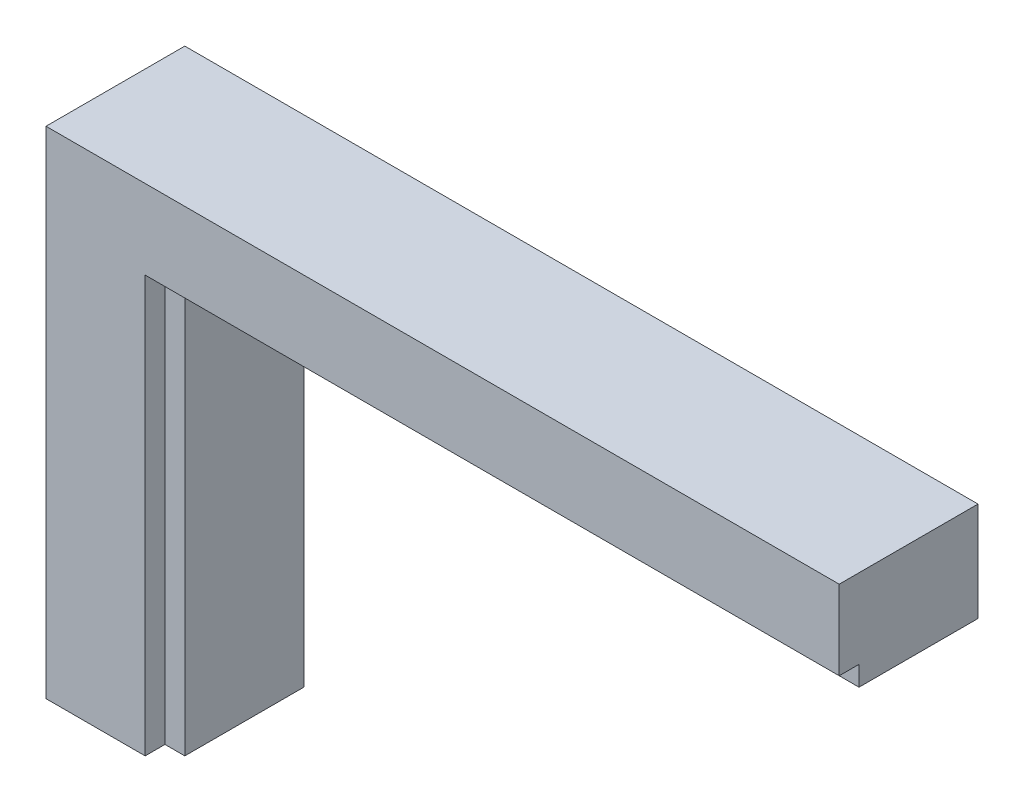
SolidWorks part; units mm, degrees
ref_plane "Спереди" through (0, 0, 0) normal (0, 0, 1) x (1, 0, 0)
ref_plane "Сверху" through (0, 0, 0) normal (0, 1, 0) x (1, 0, 0)
ref_plane "Справа" through (0, 0, 0) normal (1, 0, 0) x (0, 0, -1)
sketch "Эскиз2" plane through (0, 0, 0) normal (0, 0, 1) x (1, 0, 0)
  line L0 (0, 0) -> (0, 250)
  line L1 (0, 250) -> (400, 250)
  line L2 (400, 250) -> (400, 200)
  line L3 (400, 200) -> (60, 200)
  line L4 (60, 200) -> (60, 0)
  line L5 (60, 0) -> (0, 0)
extrude "Бобышка-Вытянуть1" add sketch "Эскиз2" along normal blind 70
sketch "Эскиз3" plane through (0, 0, 0) normal (0, -1, 0) x (1, 0, 0)
  line L1 (60, 70) -> (50, 70)
  line L2 (60, 70) -> (60, 60)
  line L3 (60, 60) -> (50, 60)
  line L4 (50, 70) -> (50, 60)
extrude "Вырез-Вытянуть1" cut sketch "Эскиз3" against normal blind 210
sketch "Эскиз4" plane through (400, 0, 0) normal (1, 0, 0) x (0, 0, -1)
  line L1 (-70, 200) -> (-60, 200)
  line L2 (-70, 200) -> (-70, 210)
  line L3 (-70, 210) -> (-60, 210)
  line L4 (-60, 200) -> (-60, 210)
extrude "Вырез-Вытянуть2" cut sketch "Эскиз4" against normal blind 340
